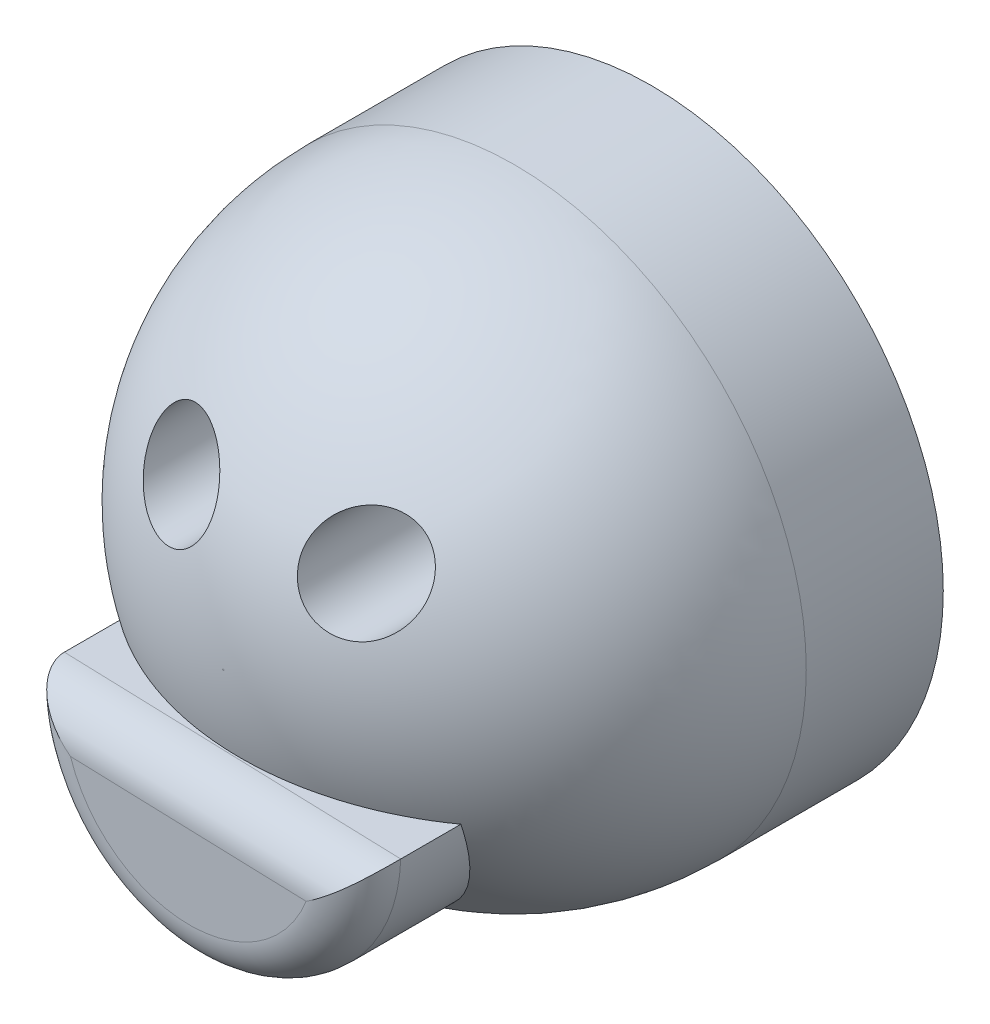
SolidWorks part; units mm, degrees
ref_plane "Front Plane" through (0, 0, 0) normal (0, 0, 1) x (1, 0, 0)
ref_plane "Top Plane" through (0, 0, 0) normal (0, 1, 0) x (1, 0, 0)
ref_plane "Right Plane" through (0, 0, 0) normal (1, 0, 0) x (0, 0, -1)
sketch "Sketch1" plane through (0, 0, 0) normal (0, 0, 1) x (1, 0, 0)
  circle A0 centre (0, 0) radius 34.075
  dimension "D1" = 68.15
extrude "Boss-Extrude1" add sketch "Sketch1" along normal blind 50
fillet "Fillet1" radius 34 1 edges at (34.075, 0, 50)
sketch "Sketch3" plane through (0, 0, 0) normal (0, 0, -1) x (-1, 0, 0)
  circle A0 centre (-11.4272, 12.8505) radius 5.5
  circle A1 centre (9.2574, 12.8505) radius 5.5
  dimension "D1" = 11
  dimension "D2" = 11
extrude "Cut-Extrude1" cut sketch "Sketch3" against normal blind 57
sketch "Sketch4" plane through (0, 0, 0) normal (0, 0, -1) x (-1, 0, 0)
  line L0 (-19.7214, -9.7757) -> (19.5559, -8.5017)
  arc A0 (-19.7214, -9.7757) -> (19.5559, -8.5017) centre (-0.0828, -9.1387) ccw
extrude "Boss-Extrude2" add sketch "Sketch4" against normal blind 54
fillet "Fillet2" radius 5 2 edges at (0.0828, -9.1387, 54) (-0.5543, -28.7773, 54)
sketch "Sketch5" plane through (0, 0, 0) normal (0, 0, -1) x (-1, 0, 0)
  circle A0 centre (0, 0) radius 28.2539
extrude "Cut-Extrude2" cut sketch "Sketch5" against normal blind 27
